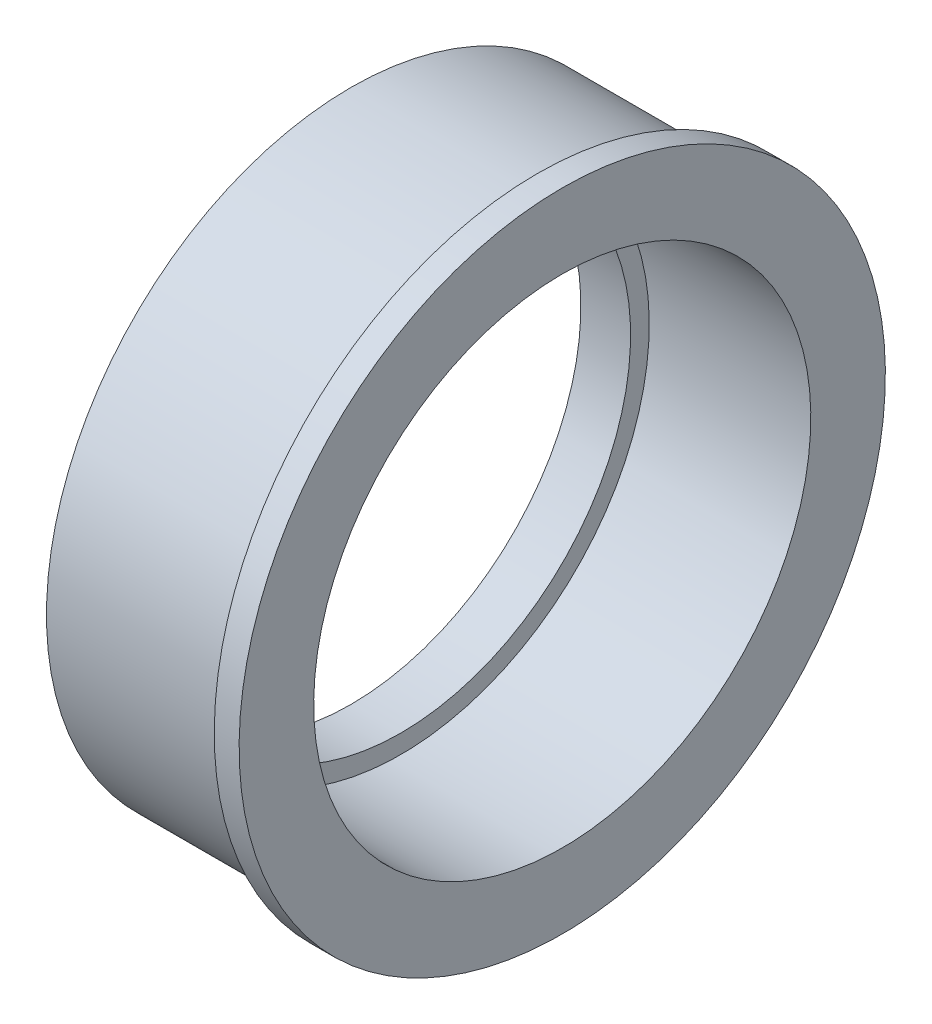
SolidWorks part; units mm, degrees
ref_plane "Face" through (0, 0, 0) normal (0, 0, 1) x (1, 0, 0)
ref_plane "Dessus" through (0, 0, 0) normal (0, 1, 0) x (1, 0, 0)
ref_plane "Droite" through (0, 0, 0) normal (1, 0, 0) x (0, 0, -1)
sketch "Esquisse1" plane through (0, 0, 0) normal (0, 0, 1) x (1, 0, 0)
  line L0 (81.2775, 0) -> (-76.6571, 0) construction
  line L1 (4, 20) -> (17, 20)
  line L2 (17, 26) -> (15, 26)
  line L3 (15, 26) -> (15, 24.5)
  line L4 (15, 24.5) -> (0, 24.5)
  line L5 (0, 24.5) -> (0, 18.5)
  line L6 (4, 20) -> (4, 18.5)
  line L7 (17, 20) -> (17, 20.0595)
  line L8 (17, 20.0595) -> (17, 26)
  line L11 (0, 18.5) -> (4, 18.5)
  dimension "D1" = 20
  dimension "D2" = 17
  dimension "D3" = 2
  dimension "D4" = 26
  dimension "D5" = 24.5
  dimension "D6" = 18.5
  dimension "D8" = 4
revolve "Révolution8" add sketch "Esquisse1" angle 360 about L0
